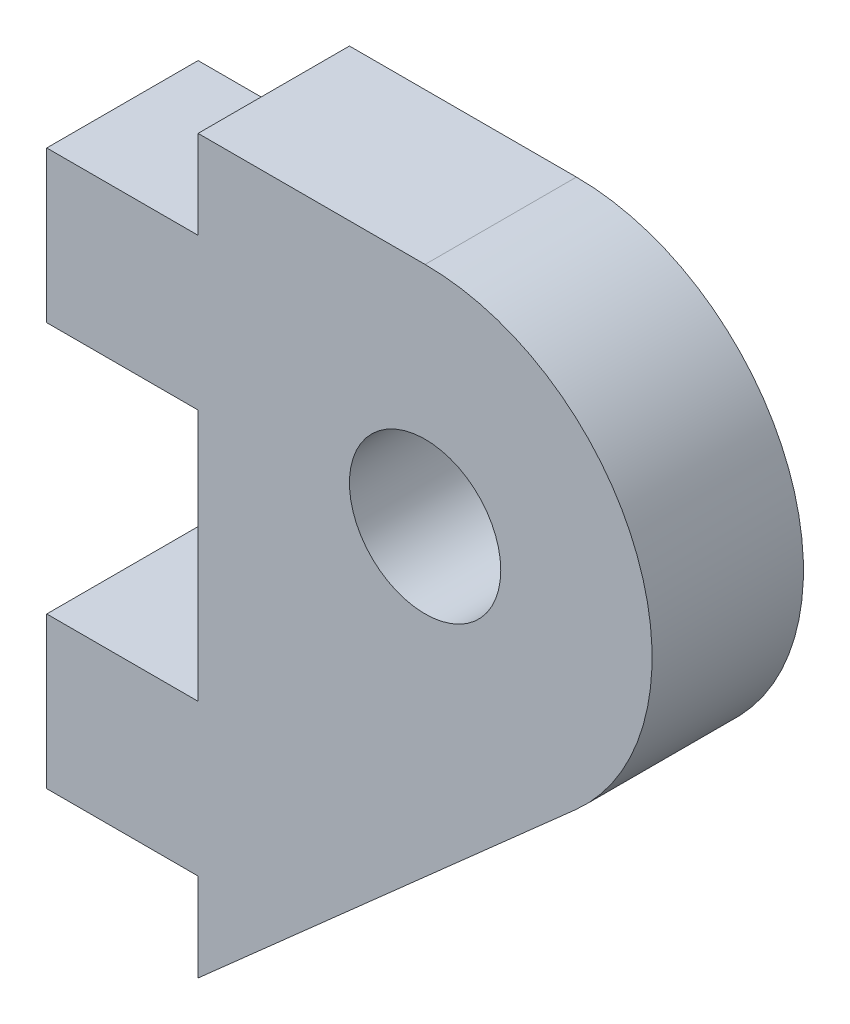
SolidWorks part; units mm, degrees
ref_plane "Front Plane" through (0, 0, 0) normal (0, 0, 1) x (1, 0, 0)
ref_plane "Top Plane" through (0, 0, 0) normal (0, 1, 0) x (1, 0, 0)
ref_plane "Right Plane" through (0, 0, 0) normal (1, 0, 0) x (0, 0, -1)
sketch "Sketch1" plane through (0, 0, 0) normal (0, 0, 1) x (1, 0, 0)
  line L0 (0, 0) -> (0, 10)
  line L1 (0, 10) -> (4.5, 10) construction
  line L2 (7.4844, 6.632) -> (0, 0)
  line L3 (4.5, 14.5) -> (0, 14.5)
  line L4 (0, 14.5) -> (0, 10)
  circle A0 centre (4.5, 10) radius 1.5
  arc A1 (7.4844, 6.632) -> (4.5, 14.5) centre (4.5, 10) ccw
  dimension "D2" = 4.5
  dimension "D3" = 3
  dimension "D1" = 10
extrude "Boss-Extrude1" add sketch "Sketch1" along normal mid plane 3
sketch "Sketch2" plane through (0, 0, 0) normal (-1, 0, 0) x (0, 0, 1)
  line L0 (1.5, 7.25) -> (0, 7.25) construction
  line L1 (1.5, 14.5) -> (1.5, 0) construction
  line L2 (0, 7.25) -> (0, 11.25) construction
  line L3 (-1.5, 4.75) -> (1.5, 1.75) construction
  line L4 (-1.5, 12.75) -> (1.5, 12.75)
  line L5 (-1.5, 12.75) -> (-1.5, 9.75)
  line L6 (-1.5, 9.75) -> (1.5, 9.75)
  line L7 (1.5, 12.75) -> (1.5, 9.75)
  line L8 (-1.5, 12.75) -> (1.5, 9.75) construction
  line L9 (-1.5, 9.75) -> (1.5, 12.75) construction
  line L10 (-1.5, 1.75) -> (1.5, 4.75) construction
  line L11 (1.5, 1.75) -> (1.5, 4.75)
  line L12 (-1.5, 4.75) -> (1.5, 4.75)
  line L13 (-1.5, 1.75) -> (-1.5, 4.75)
  line L14 (-1.5, 1.75) -> (1.5, 1.75)
  dimension "D1" = 4
  dimension "D2" = 3
extrude "Boss-Extrude2" add sketch "Sketch2" along normal blind 3
